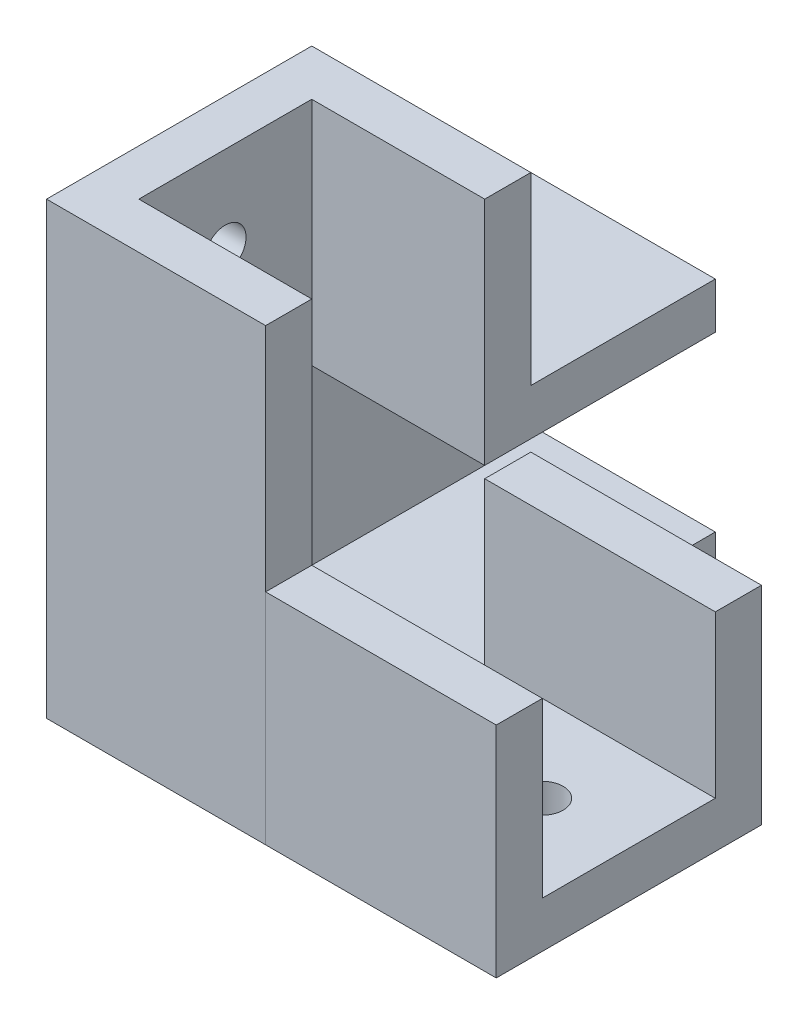
SolidWorks part; units mm, degrees
ref_plane "前视基准面" through (0, 0, 0) normal (0, 0, 1) x (1, 0, 0)
ref_plane "上视基准面" through (0, 0, 0) normal (0, 1, 0) x (1, 0, 0)
ref_plane "右视基准面" through (0, 0, 0) normal (1, 0, 0) x (0, 0, -1)
sketch "草图1" plane through (0, 0, 0) normal (0, 0, 1) x (1, 0, 0)
  line L1 (-4, 19) -> (0, 19)
  line L2 (-4, 19) -> (-4, 0)
  line L3 (-4, 0) -> (0, 0)
  line L4 (0, 19) -> (0, 0)
  line L5 (0, 0) -> (15, 0)
  line L6 (0, 0) -> (0, 4)
  line L7 (0, 4) -> (15, 4)
  line L8 (15, 0) -> (15, 4)
  dimension "D1" = 4
  dimension "D2" = 4
  dimension "D3" = 15
  dimension "D4" = 15
extrude "凸台-拉伸1" add sketch "草图1" along normal blind 15 contours L4 L1 L2 L3 | L5 L8 L7 L4
sketch "草图2" plane through (0, 0, 15) normal (0, 0, 1) x (1, 0, 0)
  line L1 (-4, 19) -> (15, 19)
  line L2 (-4, 19) -> (-4, 0)
  line L3 (-4, 0) -> (15, 0)
  line L4 (15, 19) -> (15, 0)
extrude "凸台-拉伸2" add sketch "草图2" along normal blind 4
sketch "草图3" plane through (0, 0, 0) normal (0, 0, -1) x (-1, 0, 0)
  line L1 (0, 19) -> (4, 19)
  line L2 (0, 19) -> (0, 0)
  line L3 (0, 0) -> (4, 0)
  line L4 (4, 19) -> (4, 0)
  line L5 (0, 0) -> (-15, 0)
  line L6 (0, 0) -> (0, 4)
  line L7 (0, 4) -> (-15, 4)
  line L8 (-15, 0) -> (-15, 4)
  line L13 (4, 19) -> (-15, 19)
  line L14 (4, 19) -> (4, 23)
  line L15 (4, 23) -> (-15, 23)
  line L16 (-15, 19) -> (-15, 23)
  dimension "D1" = 4
extrude "凸台-拉伸3" add sketch "草图3" along normal blind 20
sketch "草图5" plane through (15, 0, 0) normal (1, 0, 0) x (0, 0, -1)
  line L0 (-15, 4) -> (20, 4) construction
  line L1 (-19, 0) -> (-15, 0)
  line L2 (-19, 0) -> (-19, 19)
  line L3 (-19, 19) -> (-15, 19)
  line L4 (-15, 4) -> (-15, 19)
  line L5 (-15, 0) -> (0, 0)
  line L7 (-15, 4) -> (0, 4)
  line L10 (0, 0) -> (4, 0)
  line L11 (0, 4) -> (0, 18)
  line L12 (0, 18) -> (4, 18)
  line L13 (4, 0) -> (4, 18)
  line M3 (-19, 0) -> (20, 0)
  line M5 (20, 4) -> (-15, 4)
  line M6 (-15, 4) -> (-15, 19)
  line M7 (-15, 19) -> (-19, 19)
  line M8 (-19, 19) -> (-19, 0)
  dimension "D1" = 15
  dimension "D2" = 4
extrude "凸台-拉伸5" add sketch "草图5" along normal blind 20 separate body contours L4 M3 M6 M7 M8 | L13 L12 L11 M5
sketch "草图6" plane through (0, 19, 0) normal (0, 1, 0) x (1, 0, 0)
  line L0 (-4, -19) -> (-4, 0) construction
  line L1 (15, -19) -> (-4, -19)
  line L2 (15, -19) -> (15, -15)
  line L3 (15, -15) -> (0, -15)
  line L4 (-4, -19) -> (-4, -16)
  line L7 (-4, -16) -> (-4, 0)
  line L9 (0, -15) -> (0, 0)
  line L10 (-4, 0) -> (0, 0)
  line L14 (15, 3) -> (15, 0)
  line L15 (-4, 0) -> (0, 0) construction
  dimension "D1" = 3
extrude "凸台-拉伸6" add sketch "草图6" along normal blind 20 separate body
sketch "草图7" plane through (0, 23, 0) normal (0, 1, 0) x (1, 0, 0)
  line L0 (15, 20) -> (15, 0) construction
  line L1 (-4, 0) -> (15, 0)
  line L2 (-4, 0) -> (-4, 4)
  line L3 (-4, 4) -> (15, 4)
  line L4 (15, 0) -> (15, 4)
  dimension "D1" = 4
  dimension "D2" = 0
extrude "凸台-拉伸7" add sketch "草图7" along normal blind 16
sketch "草图8" plane through (-4, 0, 0) normal (-1, 0, 0) x (0, 0, 1)
  line L0 (-4, 39) -> (19, 39) construction
  line L1 (-20, 0) -> (-20, 23) construction
  circle A0 centre (7.5, 31.5) radius 1.8
  circle A1 centre (-12.5, 10.5) radius 1.8
  dimension "D2" = 3.6
  dimension "D3" = 7.5
  dimension "D4" = 3.6
  dimension "D1" = 7.5
extrude "切除-拉伸1" cut sketch "草图8" against normal blind 12
sketch "草图9" plane through (0, 0, 0) normal (0, -1, 0) x (1, 0, 0)
  line L0 (35, 19) -> (35, -4) construction
  circle A0 centre (27.5, 7.5) radius 1.8
  dimension "D1" = 3.6
  dimension "D2" = 7.5
extrude "切除-拉伸2" cut sketch "草图9" against normal blind 12
